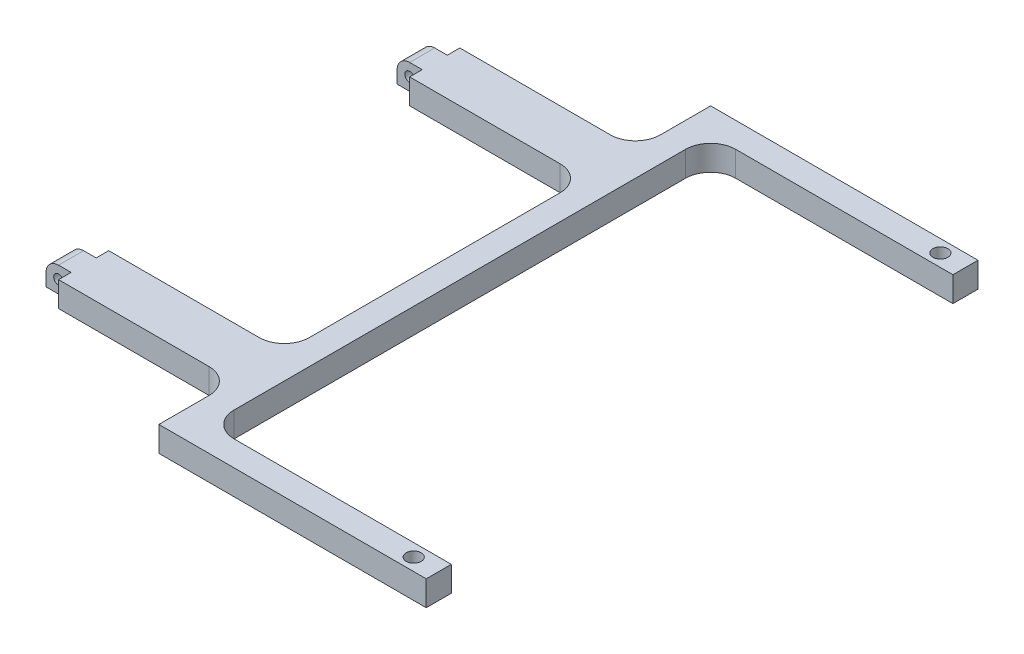
SolidWorks part; units mm, degrees
material "6061 Alloy"
ref_plane "Front Plane" through (0, 0, 0) normal (0, 0, 1) x (1, 0, 0)
ref_plane "Top Plane" through (0, 0, 0) normal (0, 1, 0) x (1, 0, 0)
ref_plane "Right Plane" through (0, 0, 0) normal (1, 0, 0) x (0, 0, -1)
sketch "Sketch1" plane through (0, 0, 0) normal (0, 1, 0) x (1, 0, 0)
  line L0 (-56.0705, 0) -> (56.0705, 0) construction
  line L1 (-56.0705, 69.85) -> (56.0705, 69.85)
  line L2 (-56.0705, 69.85) -> (-56.0705, -69.85)
  line L3 (-56.0705, -69.85) -> (56.0705, -69.85)
  line L4 (56.0705, 69.85) -> (56.0705, -69.85)
  line L6 (0, 69.85) -> (0, -69.85) construction
  dimension "D1" = 112.141
  dimension "D2" = 139.7
extrude "Extrude1" add sketch "Sketch1" along normal blind 6.35
sketch "Sketch2" plane through (0, 6.35, 0) normal (0, 1, 0) x (-1, 0, 0)
  line L0 (-56.0705, 69.85) -> (-56.0705, -69.85) construction
  line L1 (56.0705, -69.85) -> (11.6205, -69.85)
  line L2 (56.0705, -69.85) -> (56.0705, -50.8)
  line L3 (56.0705, -50.8) -> (11.6205, -50.8)
  line L4 (11.6205, -69.85) -> (11.6205, -50.8)
  line L5 (56.0705, 69.85) -> (11.6205, 69.85)
  line L6 (56.0705, 69.85) -> (56.0705, 50.8)
  line L7 (56.0705, 50.8) -> (11.6205, 50.8)
  line L8 (11.6205, 69.85) -> (11.6205, 50.8)
  line L9 (-56.0705, -63.5) -> (5.2705, -63.5)
  line L10 (-56.0705, -63.5) -> (-56.0705, 63.5)
  line L11 (-56.0705, 63.5) -> (5.2705, 63.5)
  line L12 (5.2705, -63.5) -> (5.2705, 63.5)
  line L13 (-56.0705, -69.85) -> (56.0705, -69.85) construction
  line L14 (56.0705, 69.85) -> (-56.0705, 69.85) construction
  line L15 (56.0705, -69.85) -> (56.0705, 69.85) construction
  line L16 (56.0705, -38.1) -> (11.6205, -38.1)
  line L17 (56.0705, -38.1) -> (56.0705, 38.1)
  line L18 (56.0705, 38.1) -> (11.6205, 38.1)
  line L19 (11.6205, -38.1) -> (11.6205, 38.1)
  dimension "D1" = 101.6
  dimension "D2" = 44.45
  dimension "D3" = 6.35
  dimension "D4" = 6.35
  dimension "D5" = 6.35
  dimension "D6" = 12.7
  dimension "D7" = 12.7
extrude "Cut-Extrude1" cut sketch "Sketch2" against normal blind 6.35
fillet "Fillet1" radius 6.35 6 edges at (-5.2705, 3.175, 63.5) (-5.2705, 3.175, -63.5) (-11.6205, 3.175, -50.8) (-11.6205, 3.175, 50.8) (-11.6205, 3.175, 38.1) (-11.6205, 3.175, -38.1)
sketch "Sketch5" plane through (-56.0705, 0, 0) normal (-1, 0, 0) x (0, 0, 1)
  line L0 (38.1, 0) -> (50.8, 0) construction
  line L1 (47.625, 0) -> (41.275, 0)
  line L2 (47.625, 0) -> (47.625, 6.35)
  line L3 (47.625, 6.35) -> (41.275, 6.35)
  line L4 (41.275, 0) -> (41.275, 6.35)
  line L5 (38.1, 6.35) -> (50.8, 6.35) construction
  line L6 (-50.8, 0) -> (-38.1, 0) construction
  line L7 (-41.275, 0) -> (-47.625, 0)
  line L8 (-41.275, 0) -> (-41.275, 6.35)
  line L9 (-41.275, 6.35) -> (-47.625, 6.35)
  line L10 (-47.625, 0) -> (-47.625, 6.35)
  line L11 (-50.8, 6.35) -> (-38.1, 6.35) construction
  line L12 (50.8, 0) -> (50.8, 6.35) construction
  line L13 (-38.1, 0) -> (-38.1, 6.35) construction
  point P16 (50.8, 3.175)
  dimension "D1" = 6.35
  dimension "D2" = 3.175
  dimension "D3" = 6.35
  dimension "D4" = 3.175
extrude "Extrude2" add sketch "Sketch5" along normal blind 6.35
fillet "Fillet2" radius 3.175 2 edges at (-62.4205, 6.35, -44.45) (-62.4205, 6.35, 44.45)
hole_wizard "#6 Clearance Hole1" positions "3DSketch1" profile "Sketch6" hole size "#6" standard "Ansi Inch"
sketch3d "3DSketch1"
  line L0 (-11.6205, 0, 69.85) -> (56.0705, 0, 69.85) construction
  line L1 (56.0705, 0, -63.5) -> (1.0795, 0, -63.5) construction
  line L2 (56.0705, 0, -63.5) -> (56.0705, 0, -69.85) construction
  line L3 (56.0705, 0, 69.85) -> (56.0705, 0, 63.5) construction
  point P0 (49.7205, 0, 66.675)
  point P2 (49.7205, 0, -66.675)
  dimension "D1" = 3.175
  dimension "D2" = 3.175
  dimension "D3" = 6.35
  dimension "D4" = 6.35
sketch "Sketch6" plane through (49.7205, 0, 66.675) normal (1, 0, 0) x (0, 0, -1)
  line L0 (0, 0) -> (0, 13.8408)
  line L1 (0, 13.8408) -> (1.8986, 12.7)
  line L2 (1.8986, 12.7) -> (1.8986, 0)
  line L5 (1.8986, 0) -> (0, 0)
  line L10 (0, 13.8408) -> (-1.8987, 12.7) construction
  line L11 (0, -6.35) -> (0, 107.95) construction
  dimension "Hole Dia." = 3.7973
  dimension "Hole Depth" = 12.7
  dimension "Drill Angle" = 118
hole_wizard "#2 Clearance Hole1" positions "3DSketch2" profile "Sketch8" hole size "#2" standard "Ansi Inch" end condition through all
sketch3d "3DSketch2"
  line L0 (-62.4205, 0, 47.625) -> (-56.0705, 0, 47.625) construction
  line L1 (-62.4205, 0, 47.625) -> (-62.4205, 3.175, 47.625) construction
  point P0 (-59.2455, 3.175, 47.625)
  dimension "D1" = 3.175
  dimension "D2" = 3.175
sketch "Sketch8" plane through (-59.2455, 3.175, 47.625) normal (1, 0, 0) x (0, -1, 0)
  line L0 (0, 0) -> (0, 117.475)
  line L1 (0, 117.475) -> (1.2192, 117.475)
  line L2 (1.2192, 117.475) -> (1.2192, 0)
  line L5 (1.2192, 0) -> (0, 0)
  line L11 (0, -6.35) -> (0, 107.95) construction
  dimension "Thru Hole Dia." = 2.4384
  dimension "Thru Hole Depth" = 117.475
